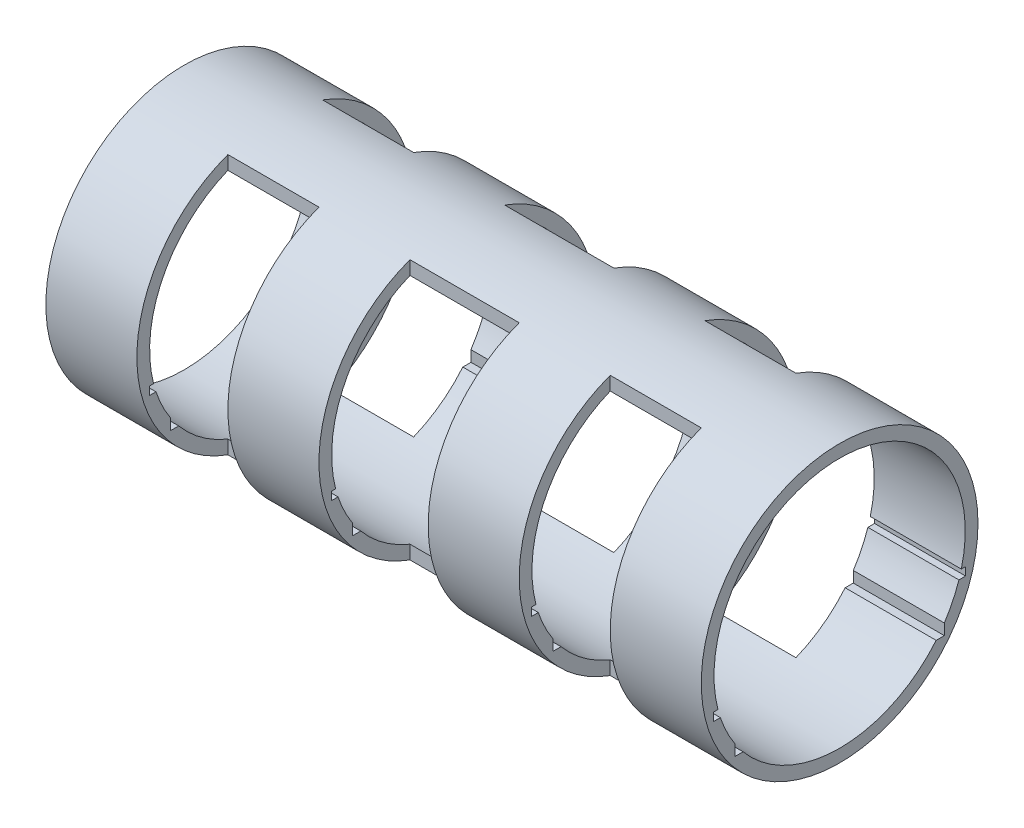
SolidWorks part; units mm, degrees
ref_plane "Front Plane" through (0, 0, 0) normal (0, 0, 1) x (1, 0, 0)
ref_plane "Top Plane" through (0, 0, 0) normal (0, 1, 0) x (1, 0, 0)
ref_plane "Right Plane" through (0, 0, 0) normal (1, 0, 0) x (0, 0, -1)
sketch "Sketch1" plane through (0, 0, 0) normal (1, 0, 0) x (0, 0, -1)
  circle A0 centre (0, 0) radius 76
  circle A1 centre (0, 0) radius 69
extrude "Boss-Extrude3" add sketch "Sketch1" along normal blind 360
sketch "Sketch2" plane through (0, 0, 0) normal (0, 1, 0) x (1, 0, 0)
  line L1 (50, 76) -> (50, 26)
  line L2 (50, 26) -> (100, 26)
  line L3 (100, 26) -> (100, 76)
  line L5 (310, 76) -> (310, 26)
  line L6 (310, 26) -> (260, 26)
  line L7 (260, 26) -> (260, 76)
  line L9 (210, 76) -> (210, 26)
  line L10 (210, 26) -> (150, 26)
  line L11 (150, 26) -> (150, 76)
  line L13 (50, 76) -> (100, 76)
  line L14 (150, 76) -> (210, 76)
  line L15 (260, 76) -> (310, 76)
  dimension "D1" = 50
  dimension "D2" = 50
  dimension "D3" = 50
  dimension "D4" = 50
  dimension "D6" = 50
  dimension "D8" = 50
extrude "Cut-Extrude1" cut sketch "Sketch2" along normal blind 125 and the other way blind 135
sketch "Sketch3" plane through (0, 0, 0) normal (0, 1, 0) x (1, 0, 0)
  line L1 (150, -76) -> (150, -26)
  line L5 (50, -76) -> (50, -26)
  line L6 (0, -76) -> (360, -76) construction
  line L7 (50, -26) -> (100, -26)
  line L8 (100, -26) -> (100, -76)
  line L9 (100, -76) -> (50, -76)
  line L10 (150, -26) -> (210, -26)
  line L11 (210, -26) -> (210, -76)
  line L12 (210, -76) -> (150, -76)
  line L14 (310, -76) -> (310, -26)
  line L15 (310, -26) -> (260, -26)
  line L16 (260, -26) -> (260, -76)
  line L17 (260, -76) -> (310, -76)
  line L18 (0, 76) -> (0, -76) construction
  line L19 (360, -76) -> (360, 76) construction
  dimension "D1" = 50
  dimension "D2" = 60
  dimension "D3" = 50
  dimension "D4" = 50
  dimension "D5" = 50
  dimension "D6" = 50
  dimension "D7" = 50
extrude "Cut-Extrude3" cut sketch "Sketch3" along normal blind 196 and the other way blind 244
sketch "Sketch4" plane through (0, 0, 0) normal (-1, 0, 0) x (0, 0, 1)
  line L8 (-57.5, -44.1588) -> (57.5, -44.1588)
  line L12 (-52.5, -41.6588) -> (-2.5, -41.6588)
  line L14 (69.1892, -17.1588) -> (69.1892, -21.6588)
  line L15 (69.1892, -21.6588) -> (57.5, -21.6588)
  line L18 (-69.1892, -21.6588) -> (-72.5294, -22.7044)
  line L26 (57.5, -44.1588) -> (57.5, -21.6588)
  line L28 (-57.5, -44.1588) -> (-60.2759, -46.2906)
  line L29 (-69.1892, -17.1588) -> (69.1892, -17.1588)
  line L30 (57.5, -44.1588) -> (60.2759, -46.2906)
  line L31 (69.1892, -21.6588) -> (72.5294, -22.7044)
  line L32 (-57.5, -44.1588) -> (-57.5, -21.6588)
  line L36 (-69.1892, -21.6588) -> (-57.5, -21.6588)
  line L37 (-69.1892, -17.1588) -> (-69.1892, -21.6588)
  line L38 (-52.5, -17.1588) -> (-2.5, -17.1588)
  line L41 (2.5, -17.1588) -> (52.5, -17.1588)
  line L43 (-2.5, -41.6588) -> (-2.5, -17.1588)
  line L44 (2.5, -17.1588) -> (2.5, -41.6588)
  line L45 (52.5, -41.6588) -> (52.5, -17.1588)
  line L46 (-52.5, -17.1588) -> (-52.5, -41.6588)
  line L47 (2.5, -41.6588) -> (52.5, -41.6588)
  circle A0 centre (0, 0) radius 76 construction
  point P6 (0, -44.1588)
  point P12 (0, -17.1588)
  point P31 (0, -41.6588)
  circle M53 centre (0, 0) radius 69
  dimension "D2" = 5
  dimension "D3" = 5
  dimension "D4" = 115
  dimension "D5" = 3.5
  dimension "D6" = 3.5
  dimension "D7" = 3.5
  dimension "D8" = 3.5
  dimension "D9" = 22.5
  dimension "D10" = 22.5
  dimension "D11" = 5
  dimension "D12" = 24.5
  dimension "D13" = 138.3784
  dimension "D14" = 4.5
  dimension "D15" = 24.5
  dimension "D16" = 50
  dimension "D17" = 50
  dimension "D18" = 11.6892
  dimension "D19" = 11.6892
extrude "Cut-Extrude4" cut sketch "Sketch4" against normal blind 404 contours L29 L37 L36 M53 | L32 L8 M53 | L8 L26 M53 | L29 L15 L14 M53
